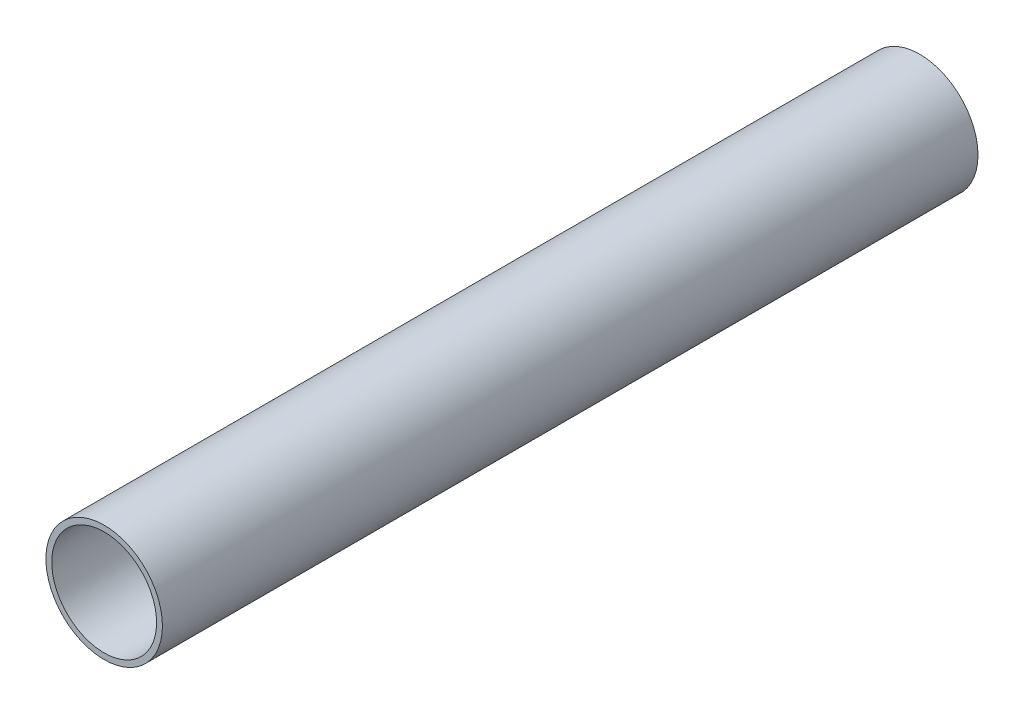
SolidWorks part; units mm, degrees
material "ABS"
ref_plane "Front Plane" through (0, 0, 0) normal (0, 0, 1) x (1, 0, 0)
ref_plane "Top Plane" through (0, 0, 0) normal (0, 1, 0) x (1, 0, 0)
ref_plane "Right Plane" through (0, 0, 0) normal (1, 0, 0) x (0, 0, -1)
sketch "Sketch3" plane through (0, 0, 0) normal (0, 0, 1) x (1, 0, 0)
  circle A0 centre (0, 0) radius 10
  dimension "D1" = 20
extrude "Extrude-Thin2" add sketch "Sketch3" along normal blind 140 thin contours A0 thin type one direction reverse wall 1
